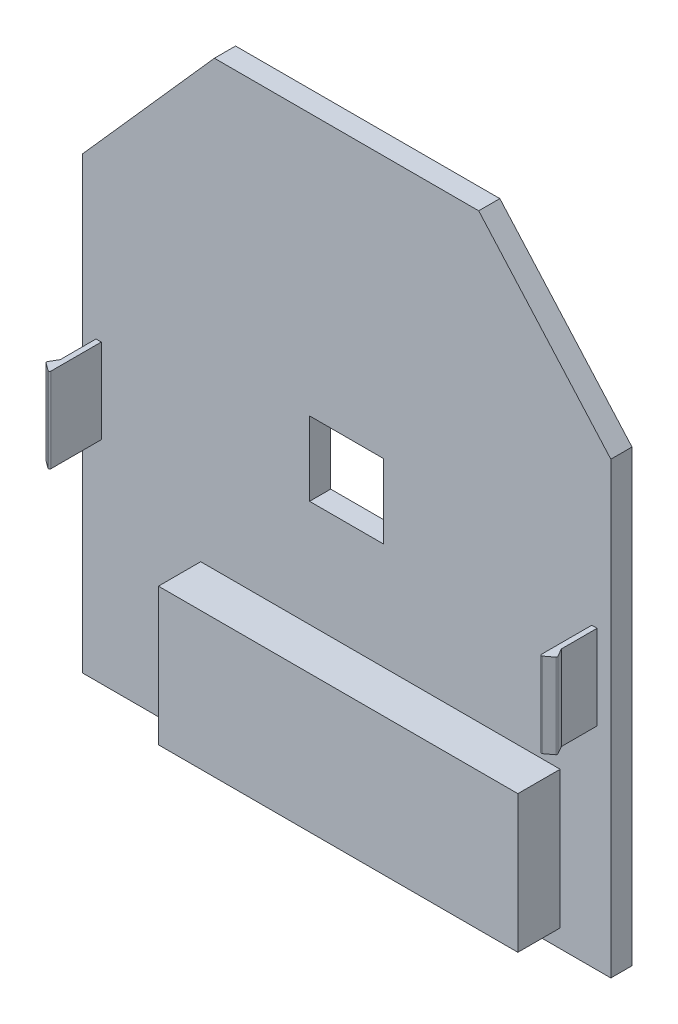
SolidWorks part; units mm, degrees
ref_plane "Plan de face" through (0, 0, 0) normal (0, 0, 1) x (1, 0, 0)
ref_plane "Plan de dessus" through (0, 0, 0) normal (0, 1, 0) x (1, 0, 0)
ref_plane "Plan de droite" through (0, 0, 0) normal (1, 0, 0) x (0, 0, -1)
sketch "Esquisse1" plane through (0, 0, 0) normal (0, 0, 1) x (1, 0, 0)
  line L0 (0, 0) -> (0, 85)
  line L1 (0, 85) -> (25, 113.2006)
  line L2 (25, 113.2006) -> (75, 113.2006)
  line L3 (75, 113.2006) -> (100, 85)
  line L4 (100, 85) -> (100, 0)
  line L5 (100, 0) -> (0, 0)
  dimension "D1" = 100
  dimension "D2" = 25
  dimension "D3" = 25
  dimension "D4" = 85
  dimension "D5" = 50
  dimension "D6" = 85
  dimension "D7" = 113.2006
extrude "Boss.-Extru.1" add sketch "Esquisse1" along normal blind 4
sketch "Esquisse4" plane through (0, 0, 4) normal (0, 0, 1) x (1, 0, 0)
  line L0 (90.41, 3.41) -> (22.41, 3.41)
  line L1 (22.41, 3.41) -> (22.41, 29.41)
  line L2 (22.41, 29.41) -> (90.41, 29.41)
  line L3 (90.41, 29.41) -> (90.41, 3.41)
  line L4 (0, 0) -> (100, 0) construction
  line L6 (0, 85) -> (0, 0) construction
  dimension "D1" = 3.41
  dimension "D2" = 68
  dimension "D3" = 26
  dimension "D4" = 22.41
extrude "Boss.-Extru.3" add sketch "Esquisse4" along normal blind 8
sketch "Esquisse8" plane through (0, 0, 0) normal (0, 0, -1) x (-1, 0, 0)
  line L0 (-43, 63.6006) -> (-43, 49.6006)
  line L1 (-43, 49.6006) -> (-57, 49.6006)
  line L2 (-57, 49.6006) -> (-57, 63.6006)
  line L3 (-57, 63.6006) -> (-43, 63.6006)
  line L4 (0, 85) -> (0, 0) construction
  line L10 (-75, 113.2006) -> (-25, 113.2006) construction
  dimension "D1" = 14
  dimension "D2" = 43
  dimension "D3" = 49.6
extrude "Enlèv. mat.-Extru.2" cut sketch "Esquisse8" against normal through all
sketch "Esquisse10" plane through (0, 0, 4) normal (0, 0, 1) x (1, 0, 0)
  line L0 (50, 0) -> (50, 113.2006) construction
  line L1 (0, 0) -> (100, 0) construction
  line L2 (75, 113.2006) -> (25, 113.2006) construction
  line L3 (3.6, 40) -> (3.6, 56)
  line L4 (3.6, 56) -> (2.6, 56)
  line L5 (2.6, 56) -> (2.6, 40)
  line L6 (2.6, 40) -> (3.6, 40)
  line L7 (0, 85) -> (0, 0) construction
  line L8 (96.4, 56) -> (97.4, 56)
  line L9 (97.4, 56) -> (97.4, 40)
  line L10 (96.4, 40) -> (96.4, 56)
  line L11 (97.4, 40) -> (96.4, 40)
  dimension "D1" = 1
  dimension "D2" = 16
  dimension "D3" = 2.6
  dimension "D4" = 40
extrude "Boss.-Extru.4" add sketch "Esquisse10" along normal blind 8.5
sketch "Esquisse13" plane through (0, 40, 0) normal (0, -1, 0) x (-1, 0, 0)
  line L0 (-97.4, -12.5) -> (-98.4, -12.5) construction
  line L1 (-98.4, -12.5) -> (-97.4, -10.7679)
  line L2 (-97.4, -12.5) -> (-97.4, -4) construction
  line L3 (-98.4, -12.5) -> (-96.4, -14)
  line L4 (-96.4, -14) -> (-96.4, -12.5)
  line L5 (-96.4, -12.5) -> (-97.4, -12.5)
  line L6 (-97.4, -12.5) -> (-97.4, -10.7679)
  dimension "D1" = 1
  dimension "D2" = 2
  dimension "D3" = 1.5
extrude "Boss.-Extru.5" add sketch "Esquisse13" against normal up to surface (16 mm away) up to face at (96.9, 56, 8.25)
sketch "Esquisse14" plane through (0, 40, 0) normal (0, -1, 0) x (1, 0, 0)
  line L0 (2.6, 12.5) -> (1.6, 12.5) construction
  line L1 (1.6, 12.5) -> (2.6, 10.7679)
  line L2 (2.6, 12.5) -> (2.6, 4) construction
  line L3 (1.6, 12.5) -> (3.6, 14)
  line L4 (3.6, 14) -> (3.6, 12.5)
  line L5 (3.6, 12.5) -> (2.6, 12.5)
  line L6 (2.6, 12.5) -> (2.6, 10.7679)
  dimension "D1" = 1
  dimension "D2" = 2
  dimension "D3" = 1.5
extrude "Boss.-Extru.6" add sketch "Esquisse14" against normal up to surface (16 mm away) up to face at (3.1, 56, 8.25)
fillet "Congé1" radius 0.25 2 edges at (98.4, 48, 12.5) (1.6, 48, 12.5)
fillet "Congé2" radius 0.25 2 edges at (96.4, 48, 14) (3.6, 48, 14)
